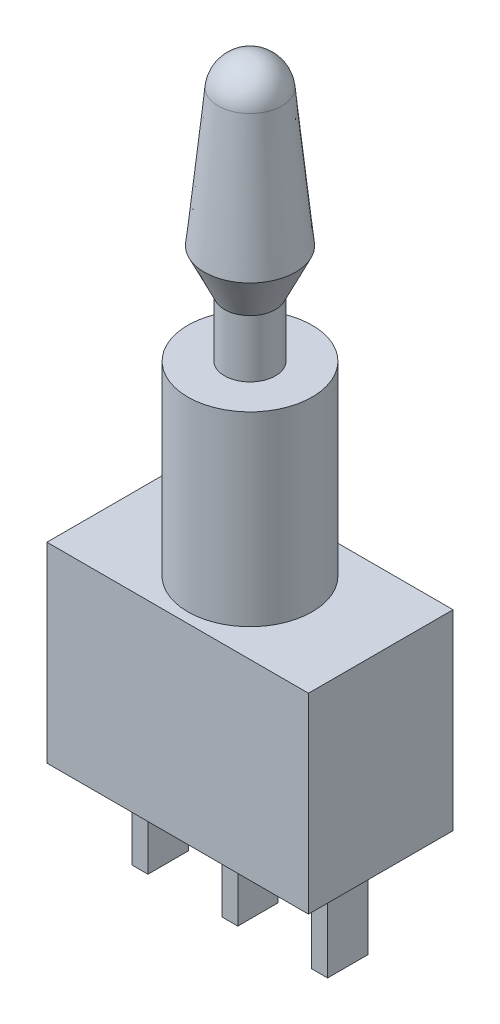
SolidWorks part; units mm, degrees
ref_plane "Front Plane" through (0, 0, 0) normal (0, 0, 1) x (1, 0, 0)
ref_plane "Top Plane" through (0, 0, 0) normal (0, 1, 0) x (1, 0, 0)
ref_plane "Right Plane" through (0, 0, 0) normal (1, 0, 0) x (0, 0, -1)
sketch "Sketch1" plane through (0, 0, 0) normal (0, 1, 0) x (1, 0, 0)
  line L1 (-6.15, -3.4) -> (6.15, -3.4)
  line L2 (-6.15, -3.4) -> (-6.15, 3.4)
  line L3 (-6.15, 3.4) -> (6.15, 3.4)
  line L4 (6.15, -3.4) -> (6.15, 3.4)
  line L5 (-6.15, -3.4) -> (6.15, 3.4) construction
  line L6 (-6.15, 3.4) -> (6.15, -3.4) construction
  point P0 (0, 0)
  dimension "D1" = 12.3
  dimension "D2" = 6.8
extrude "Boss-Extrude1" add sketch "Sketch1" along normal blind 9
sketch "Sketch2" plane through (0, 9, 0) normal (0, 1, 0) x (1, 0, 0)
  circle A0 centre (0, 0) radius 2.925
  dimension "D1" = 5.85
extrude "Boss-Extrude2" add sketch "Sketch2" along normal blind 8.75
sketch "Sketch3" plane through (0, 0, 0) normal (0, 0, 1) x (1, 0, 0)
  line L0 (0, -982.25) -> (0, 49017.75) construction
  line L1 (2.925, 17.75) -> (-2.925, 17.75) construction
  line L2 (0, 17.75) -> (1.2, 17.75)
  line L3 (1.2, 17.75) -> (1.2, 20.45)
  line L4 (1.2, 20.45) -> (2.15, 22.45)
  line L5 (2.15, 22.45) -> (1.5, 28.8937)
  line L6 (0, 30.25) -> (0, 17.75)
  arc A0 (1.5, 28.8937) -> (0, 30.25) centre (0, 28.7424) ccw
  point P5 (0, 17.75)
  dimension "D1" = 2.4
  dimension "D2" = 4.3
  dimension "D3" = 3
  dimension "D4" = 2.7
  dimension "D5" = 2
  dimension "D6" = 12.5
revolve "Revolve1" add sketch "Sketch3" angle 360 about L0
sketch "Sketch4" plane through (0, 0, 0) normal (0, -1, 0) x (1, 0, 0)
  line L0 (-4.6, 0.95) -> (4.6, 0.95) construction
  line L1 (-0.375, -0.95) -> (0.375, -0.95)
  line L2 (-0.375, -0.95) -> (-0.375, 0.95)
  line L3 (-0.375, 0.95) -> (0.375, 0.95)
  line L4 (0.375, -0.95) -> (0.375, 0.95)
  line L5 (-0.375, -0.95) -> (0.375, 0.95) construction
  line L6 (-0.375, 0.95) -> (0.375, -0.95) construction
  line L7 (-4.6, -0.95) -> (-3.85, -0.95)
  line L8 (-4.6, -0.95) -> (-4.6, 0.95)
  line L9 (-4.6, 0.95) -> (-3.85, 0.95)
  line L10 (-3.85, -0.95) -> (-3.85, 0.95)
  line L11 (-4.6, -0.95) -> (-3.85, 0.95) construction
  line L12 (-4.6, 0.95) -> (-3.85, -0.95) construction
  line L13 (3.85, -0.95) -> (4.6, -0.95)
  line L14 (3.85, -0.95) -> (3.85, 0.95)
  line L15 (3.85, 0.95) -> (4.6, 0.95)
  line L16 (4.6, -0.95) -> (4.6, 0.95)
  line L17 (3.85, -0.95) -> (4.6, 0.95) construction
  line L18 (3.85, 0.95) -> (4.6, -0.95) construction
  line L19 (-3.85, -0.95) -> (-0.375, -0.95) construction
  line L20 (0.375, -0.95) -> (3.85, -0.95) construction
  point P0 (0, 0)
  point P6 (-4.225, 0)
  point P11 (4.225, 0)
  dimension "D1" = 0.75
  dimension "D2" = 1.9
  dimension "D3" = 9.2
extrude "Boss-Extrude3" add sketch "Sketch4" along normal blind 4.6
